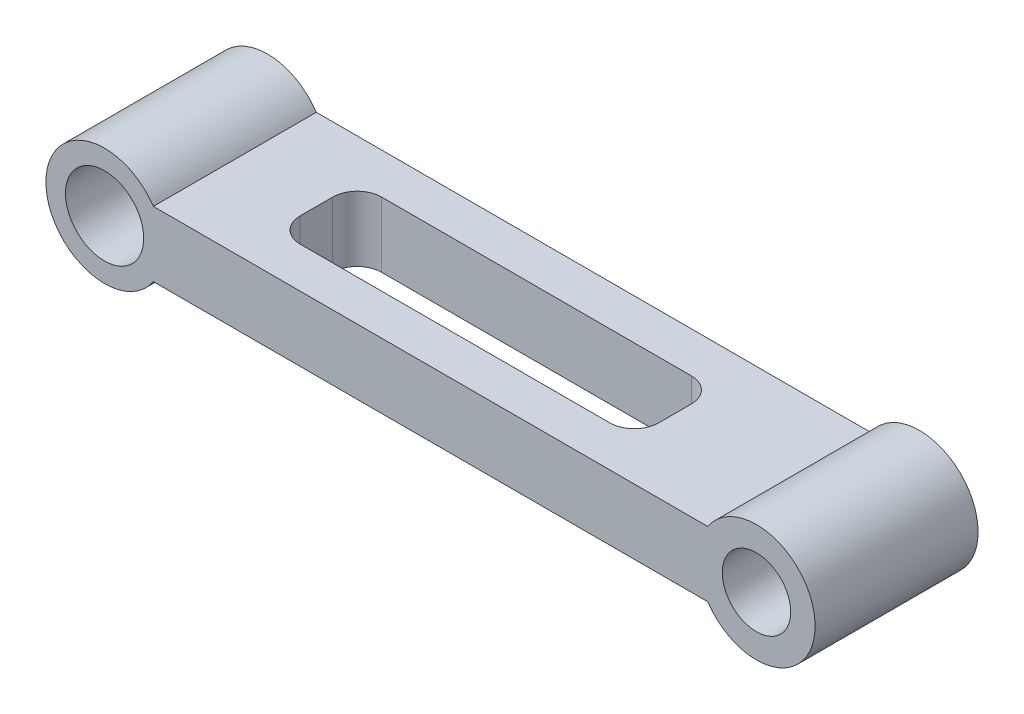
SolidWorks part; units mm, degrees
ref_plane "Front Plane" through (0, 0, 0) normal (0, 0, 1) x (1, 0, 0)
ref_plane "Top Plane" through (0, 0, 0) normal (0, 1, 0) x (1, 0, 0)
ref_plane "Right Plane" through (0, 0, 0) normal (1, 0, 0) x (0, 0, -1)
sketch "Sketch2" plane through (0, 0, 0) normal (0, 0, 1) x (1, 0, 0)
  line L2 (29.9333, 20) -> (370.0667, 20)
  line L4 (29.9333, -20) -> (370.0667, -20)
  circle A1 centre (0, 0) radius 24
  arc A2 (29.9333, 20) -> (29.9333, -20) centre (0, 0) ccw
  circle A3 centre (400, 0) radius 21
  arc A4 (370.0667, -20) -> (370.0667, 20) centre (400, 0) ccw
  dimension "D1" = 72
  dimension "D2" = 48
  dimension "D3" = 72
  dimension "D4" = 42
  dimension "D6" = 20
  dimension "D5" = 40
  dimension "D7" = 400
extrude "Boss-Extrude1" add sketch "Sketch2" along normal mid plane 100
sketch "Sketch3" plane through (0, 20, 0) normal (0, 1, 0) x (1, 0, 0)
  line L1 (95, 25) -> (285, 25)
  line L2 (80, 10) -> (80, -10)
  line L3 (95, -25) -> (285, -25)
  line L4 (300, 10) -> (300, -10)
  arc A0 (285, 25) -> (300, 10) centre (285, 10) cw
  arc A1 (80, -10) -> (95, -25) centre (95, -10) ccw
  arc A2 (285, -25) -> (300, -10) centre (285, -10) ccw
  arc A3 (95, 25) -> (80, 10) centre (95, 10) ccw
  point P7 (300, 25)
  point P12 (300, -25)
  dimension "D5" = 15
  dimension "D1" = 300
  dimension "D2" = 80
  dimension "D3" = 50
  dimension "D4" = 25
extrude "Cut-Extrude1" cut sketch "Sketch3" against normal through all
